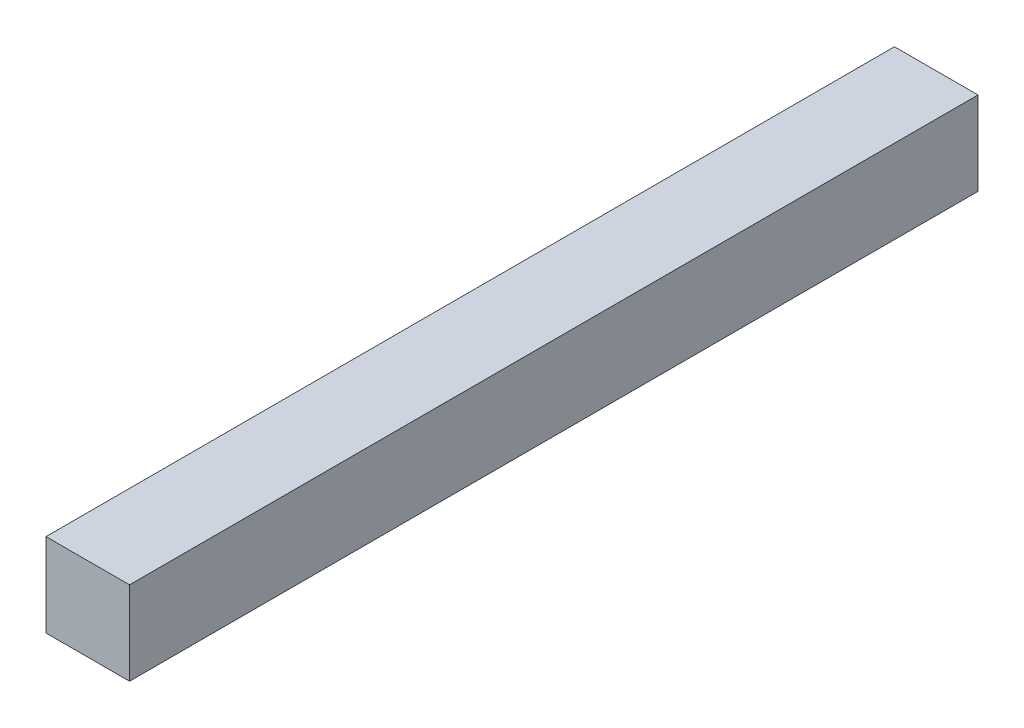
SolidWorks part; units mm, degrees
ref_plane "Front Plane" through (0, 0, 0) normal (0, 0, 1) x (1, 0, 0)
ref_plane "Top Plane" through (0, 0, 0) normal (0, 1, 0) x (1, 0, 0)
ref_plane "Right Plane" through (0, 0, 0) normal (1, 0, 0) x (0, 0, -1)
sketch "Sketch1" plane through (0, 0, 0) normal (0, 0, 1) x (1, 0, 0)
  line L1 (5, 5) -> (-5, 5)
  line L2 (5, 5) -> (5, -5)
  line L3 (5, -5) -> (-5, -5)
  line L4 (-5, 5) -> (-5, -5)
  line L5 (5, 5) -> (-5, -5) construction
  line L6 (5, -5) -> (-5, 5) construction
  point P0 (0, 0)
  dimension "D1" = 10
extrude "Boss-Extrude1" add sketch "Sketch1" along normal blind 101.6025
sketch "Sketch3" plane through (0, 0, 0) normal (0, 0, -1) x (-1, 0, 0)
  point P0 (0, 0)
sketch "Sketch4" plane through (0, 0, 101.6025) normal (0, 0, 1) x (1, 0, 0)
  line L1 (0, 0) -> (0, -18.82) construction
  point P5 (0, 0)
  point P8 (0, 0)
  dimension "D1" = 18.82
sketch "Sketch7" plane through (0, -5, 0) normal (0, -1, 0) x (-1, 0, 0)
  line L0 (0, -91.6025) -> (0, -101.6025)
  line L1 (0.2486, -106.5963) -> (-0.2486, -96.6087) construction
  line L2 (-5, -101.6025) -> (-5, 0) construction
  dimension "D1" = 10
